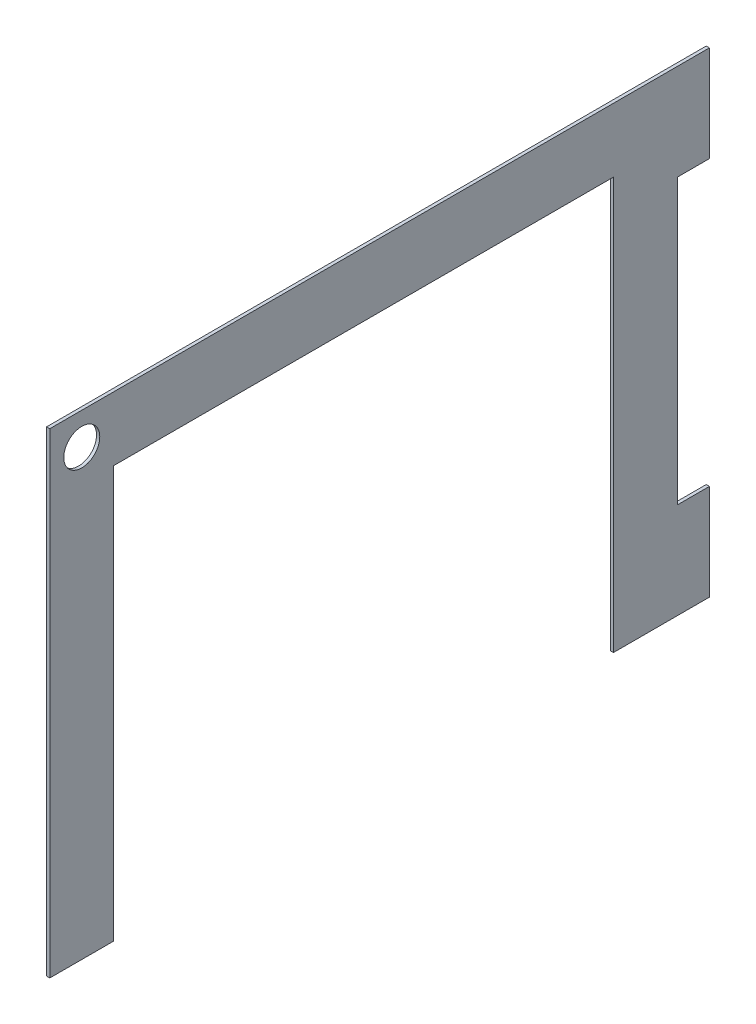
SolidWorks part; units mm, degrees
ref_plane "Front Plane" through (0, 0, 0) normal (0, 0, 1) x (1, 0, 0)
ref_plane "Top Plane" through (0, 0, 0) normal (0, 1, 0) x (1, 0, 0)
ref_plane "Right Plane" through (0, 0, 0) normal (1, 0, 0) x (0, 0, -1)
sketch "Sketch1" plane through (0, 0, 0) normal (1, 0, 0) x (0, 0, -1)
  line L0 (-201.1349, -254) -> (-201.1349, 123.825)
  line L5 (322.7464, -177.8) -> (322.7464, -254)
  line L6 (297.3464, 47.625) -> (297.3464, -177.8)
  line L7 (-201.1349, 123.825) -> (297.3464, 123.825)
  line L9 (297.3464, -254) -> (246.5464, -254)
  line L10 (246.5464, -254) -> (246.5464, 73.025)
  line L11 (246.5464, 73.025) -> (-150.3349, 73.025)
  line L12 (-150.3349, 73.025) -> (-150.3349, -254)
  line L13 (-150.3349, -254) -> (-201.1349, -254)
  line L14 (297.3464, 123.825) -> (322.7464, 123.825)
  line L15 (322.7464, 123.825) -> (322.7464, 47.625)
  line L16 (322.7464, 47.625) -> (297.3464, 47.625)
  line L17 (297.3464, -254) -> (322.7464, -254)
  line L18 (322.7464, -177.8) -> (297.3464, -177.8)
  circle A0 centre (-175.7349, 98.425) radius 14.2875
  point P0 (0, 0)
  dimension "D2" = 76.2
  dimension "D3" = 76.2
  dimension "D10" = 28.575
  dimension "D4" = 50.8
  dimension "D5" = 50.8
  dimension "D6" = 377.825
extrude "Boss-Extrude1" add sketch "Sketch1" along normal mid plane 2.54
